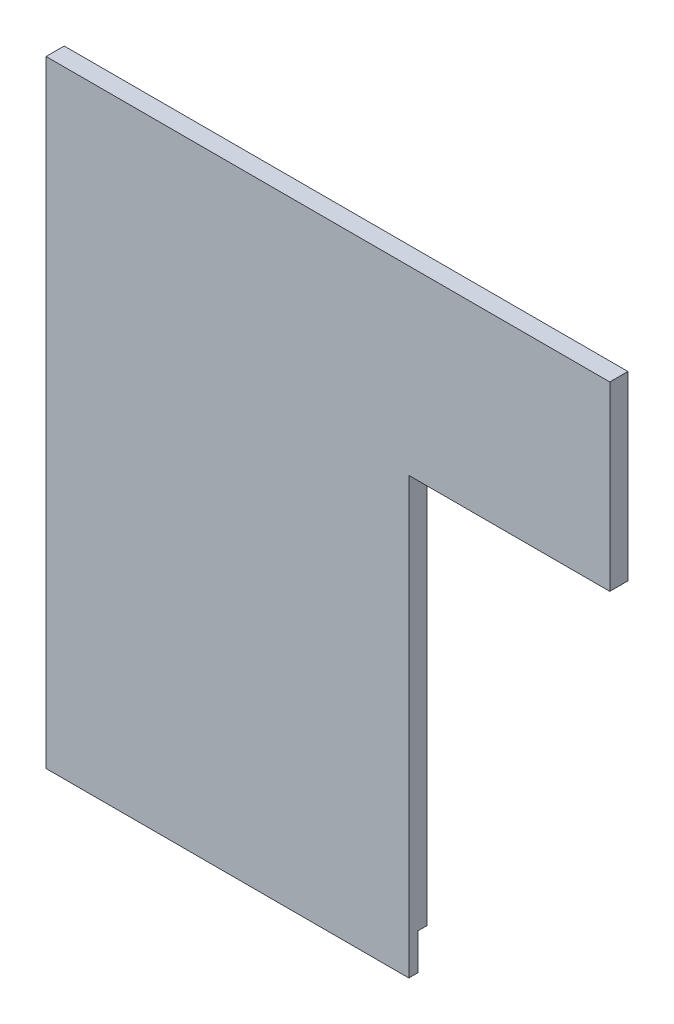
SolidWorks part; units mm, degrees
ref_plane "Front Plane" through (0, 0, 0) normal (0, 0, 1) x (1, 0, 0)
ref_plane "Top Plane" through (0, 0, 0) normal (0, 1, 0) x (1, 0, 0)
ref_plane "Right Plane" through (0, 0, 0) normal (1, 0, 0) x (0, 0, -1)
sketch "Sketch1" plane through (0, 0, 0) normal (0, 0, 1) x (1, 0, 0)
  line L1 (0, 0) -> (63.5, 0)
  line L2 (0, 0) -> (0, 107.95)
  line L3 (0, 107.95) -> (63.5, 107.95)
  line L4 (63.5, 0) -> (63.5, 76.2)
  line L5 (63.5, 107.95) -> (98.679, 107.95)
  line L7 (63.5, 76.2) -> (98.679, 76.2)
  line L8 (98.679, 107.95) -> (98.679, 76.2)
  point P8 (0, 0)
  point P9 (0, 0)
  dimension "D1" = 107.95
  dimension "D2" = 63.5
  dimension "D3" = 35.179
  dimension "D4" = 76.2
extrude "Boss-Extrude1" add sketch "Sketch1" along normal blind 3.175
sketch "Sketch3" plane through (0, 0, 0) normal (0, 0, -1) x (-1, 0, 0)
  line L0 (0, 107.95) -> (0, 0) construction
  line L1 (-63.5, 0) -> (0, 0)
  line L2 (-63.5, 0) -> (-63.5, 6.35)
  line L3 (-63.5, 6.35) -> (0, 6.35)
  line L4 (0, 0) -> (0, 6.35)
  dimension "D1" = 6.35
extrude "Cut-Extrude2" cut sketch "Sketch3" against normal blind 1.5875
